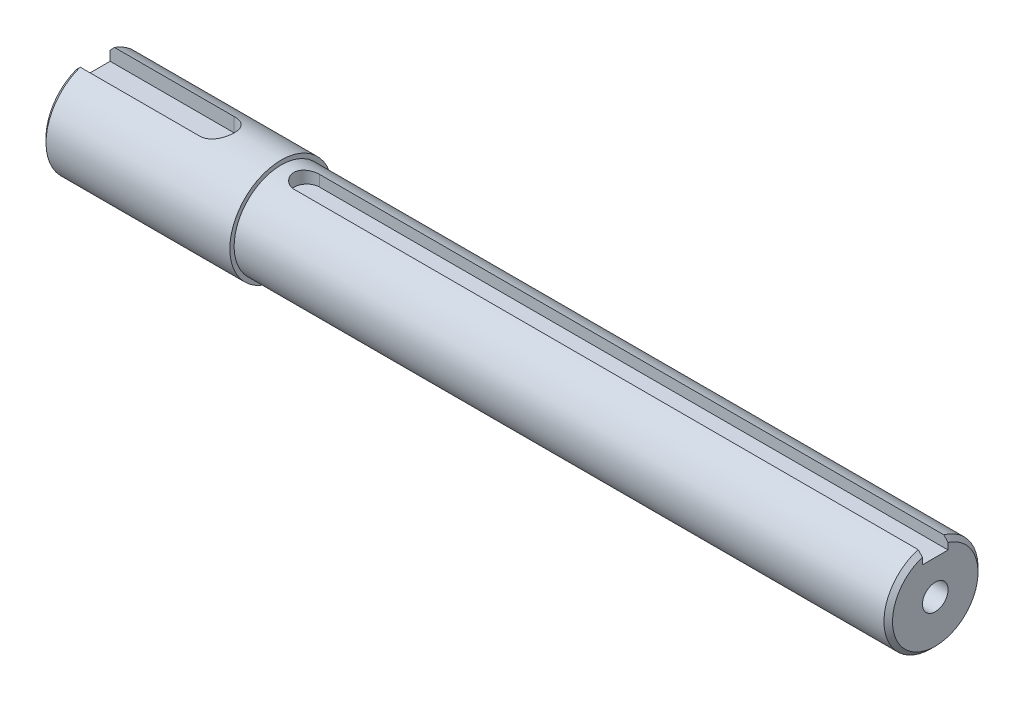
SolidWorks part; units mm, degrees
ref_plane "Front Plane" through (0, 0, 0) normal (0, 0, 1) x (1, 0, 0)
ref_plane "Top Plane" through (0, 0, 0) normal (0, 1, 0) x (1, 0, 0)
ref_plane "Right Plane" through (0, 0, 0) normal (1, 0, 0) x (0, 0, -1)
sketch "Sketch1" plane through (0, 0, 0) normal (0, 0, 1) x (1, 0, 0)
  line L0 (0, 0) -> (-197, 0)
  line L1 (-197, 0) -> (-197, 12)
  line L2 (-197, 12) -> (-153, 12)
  line L3 (-153, 12) -> (-153, 11)
  line L4 (-153, 11) -> (0, 11)
  line L5 (0, 11) -> (0, 0)
  dimension "D1" = 12
  dimension "D2" = 11
  dimension "D3" = 44
  dimension "D4" = 197
revolve "Revolve1" add sketch "Sketch1" angle 360 about L0
ref_plane "Plane1" through (0, 12, 0) normal (0, 1, 0) x (1, 0, 0)
sketch "Sketch2" plane through (0, 12, 0) normal (0, 1, 0) x (1, 0, 0)
  line L0 (-197, 0) -> (-167.9972, 0) construction
  line L1 (-197, 12) -> (-197, -12) construction
  line L2 (-167.9972, 4) -> (-197, 4)
  line L3 (-197, 4) -> (-197, -4)
  line L4 (-197, -4) -> (-167.9972, -4)
  line L5 (-163.9972, 0) -> (-167.4541, -4.4217) construction
  arc A0 (-167.9972, 4) -> (-167.9972, -4) centre (-167.9972, 0) cw
  dimension "D2" = 4
  dimension "D3" = 26
  dimension "D1" = 4
extrude "Cut-Extrude1" cut sketch "Sketch2" against normal blind 4
ref_plane "Plane2" through (0, 11, 0) normal (0, 1, 0) x (1, 0, 0)
sketch "Sketch3" plane through (0, 11, 0) normal (0, 1, 0) x (1, 0, 0)
  line L0 (0, 0) -> (-147, 0) construction
  line L1 (-147, 3) -> (0, 3)
  line L2 (0, -11) -> (0, 11) construction
  line L3 (-147, -3) -> (0, -3)
  line L4 (0, -3) -> (0, 3)
  line L5 (-150, 0) -> (-150, 4.9246) construction
  arc A0 (-147, 3) -> (-147, -3) centre (-147, 0) ccw
  point P11 (0, 0)
  dimension "D1" = 3
  dimension "D2" = 150
extrude "Cut-Extrude2" cut sketch "Sketch3" against normal blind 3
chamfer "Chamfer1" distance 1 angle 45 2 edges at (0, -11, 0) (-197, -12, 0)
sketch "Sketch4" plane through (0, 0, 0) normal (1, 0, 0) x (0, 0, -1)
  circle A0 centre (0, 0) radius 3
  dimension "D1" = 6
extrude "Cut-Extrude3" cut sketch "Sketch4" against normal blind 20
